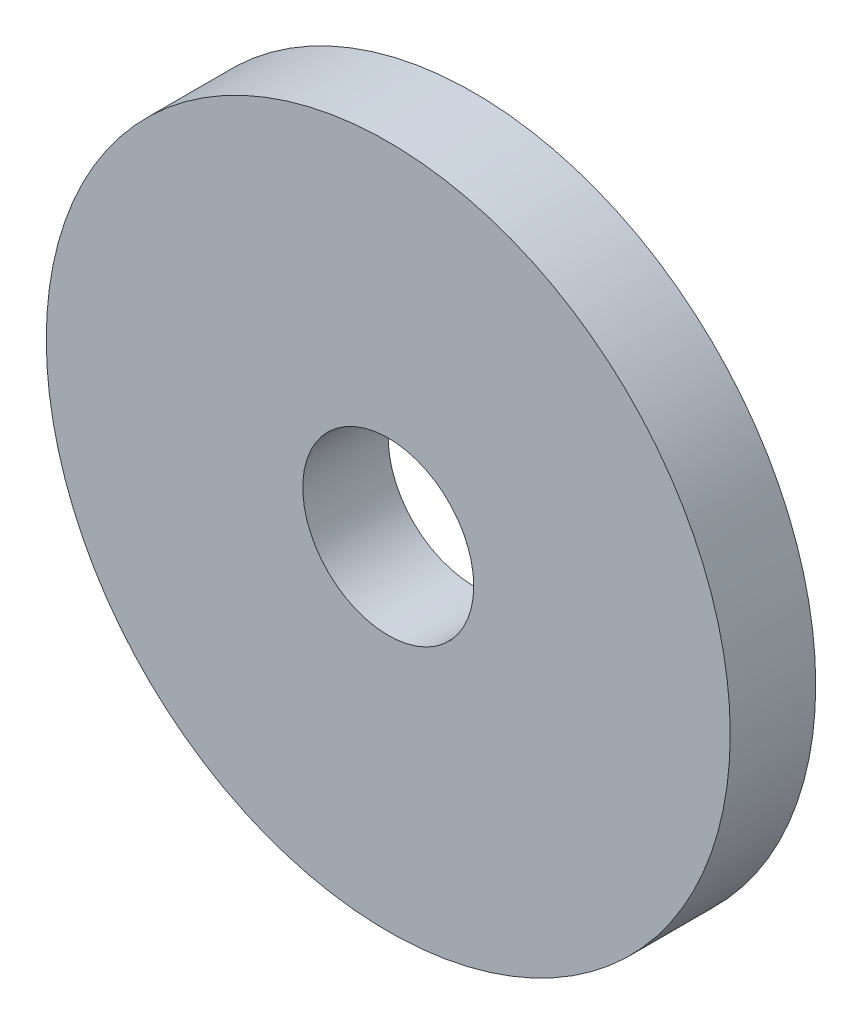
SolidWorks part; units mm, degrees
ref_plane "Front Plane" through (0, 0, 0) normal (0, 0, 1) x (1, 0, 0)
ref_plane "Top Plane" through (0, 0, 0) normal (0, 1, 0) x (1, 0, 0)
ref_plane "Right Plane" through (0, 0, 0) normal (1, 0, 0) x (0, 0, -1)
sketch "Sketch1" plane through (0, 0, 0) normal (0, 0, 1) x (1, 0, 0)
  circle A0 centre (0, 0) radius 40
  dimension "D1" = 80
extrude "Boss-Extrude1" add sketch "Sketch1" against normal blind 10
sketch "Sketch2" plane through (0, 0, 0) normal (0, 0, 1) x (1, 0, 0)
  circle A0 centre (0, 0) radius 10
  dimension "D1" = 20
extrude "Cut-Extrude1" cut sketch "Sketch2" against normal through all
